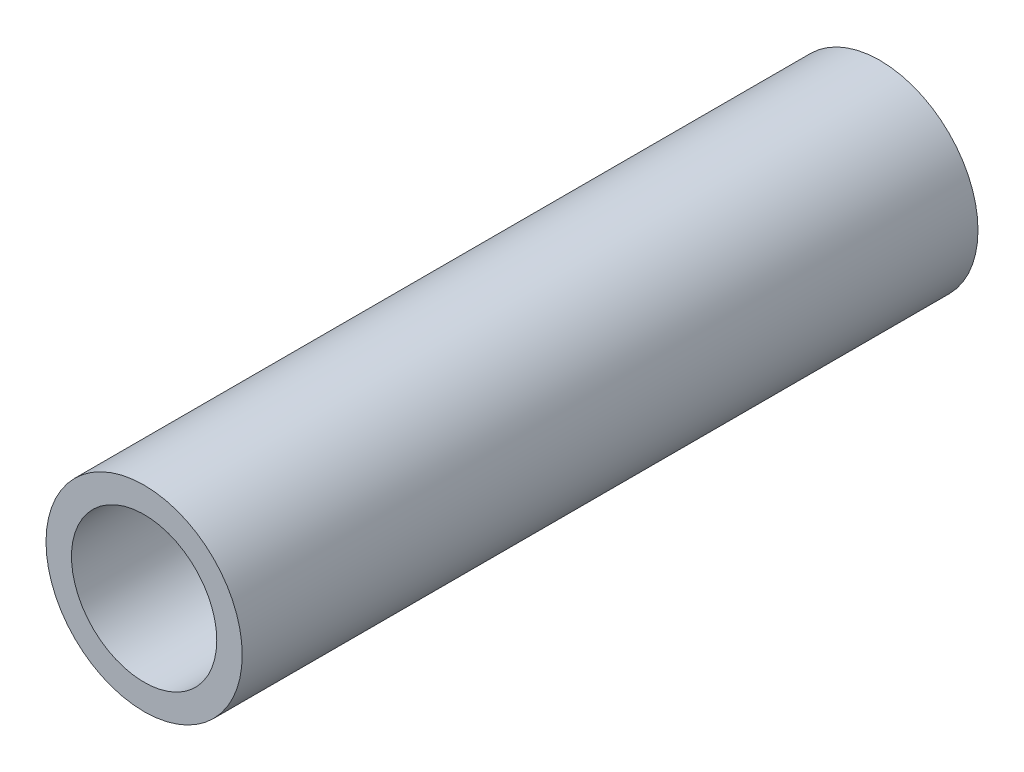
SolidWorks part; units mm, degrees
ref_plane "Front Plane" through (0, 0, 0) normal (0, 0, 1) x (1, 0, 0)
ref_plane "Top Plane" through (0, 0, 0) normal (0, 1, 0) x (1, 0, 0)
ref_plane "Right Plane" through (0, 0, 0) normal (1, 0, 0) x (0, 0, -1)
sketch "Sketch1" plane through (0, 0, 0) normal (0, 0, 1) x (1, 0, 0)
  circle A0 centre (0, 0) radius 10.668
  dimension "Pipe OD" = 21.336
extrude "Extrude-Thin1" add sketch "Sketch1" along normal mid plane 80 thin thin type one direction reverse wall 2.7686
